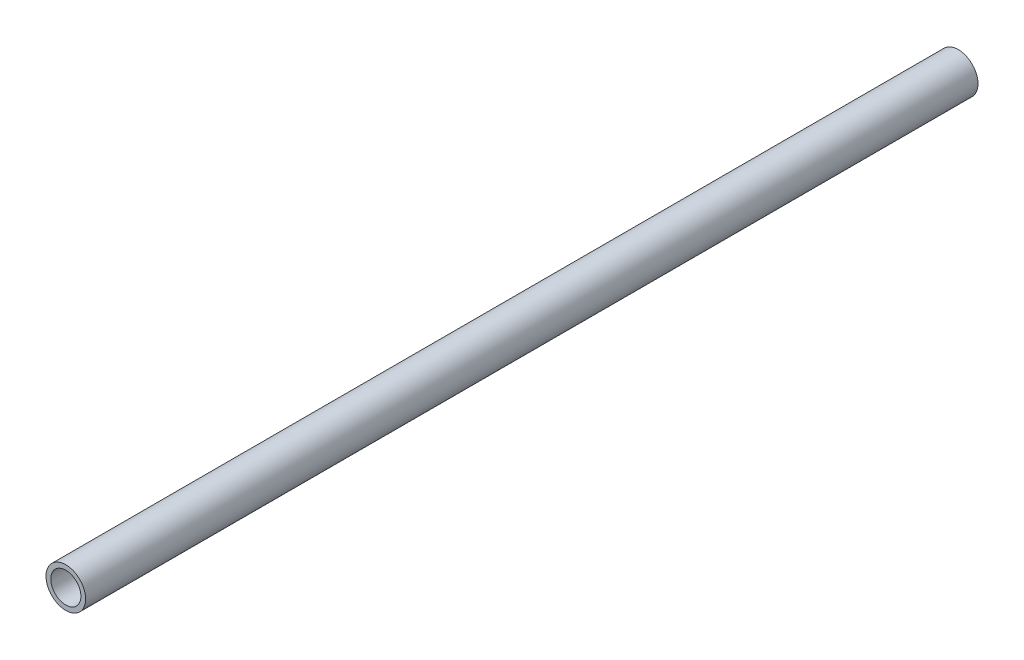
SolidWorks part; units mm, degrees
material "carbon"
ref_plane "Płaszczyzna XY" through (0, 0, 0) normal (0, 0, 1) x (1, 0, 0)
ref_plane "Płaszczyzna XZ" through (0, 0, 0) normal (0, 1, 0) x (1, 0, 0)
ref_plane "Płaszczyzna YZ" through (0, 0, 0) normal (1, 0, 0) x (0, 0, -1)
sketch "Szkic1" plane through (0, 0, 0) normal (0, 0, 1) x (1, 0, 0)
  circle A0 centre (0, 0) radius 6.35
  circle A1 centre (0, 0) radius 8.35
  dimension "D1" = 12.7
  dimension "D2" = 16.7
extrude "Dodanie-wyciągnięcie1" add sketch "Szkic1" along normal up to surface (374.7168 mm away) and the other way up to surface (1.2184 mm away)
